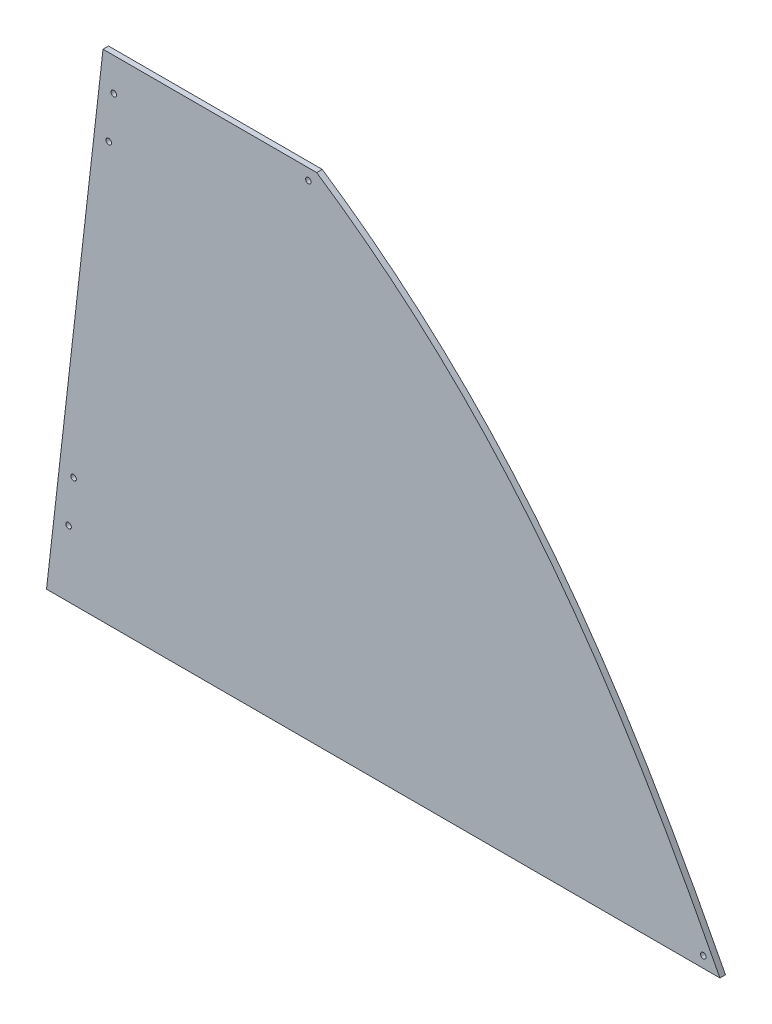
SolidWorks part; units mm, degrees
material "PC High Viscosity"
ref_plane "Front Plane" through (0, 0, 0) normal (0, 0, 1) x (1, 0, 0)
ref_plane "Top Plane" through (0, 0, 0) normal (0, 1, 0) x (1, 0, 0)
ref_plane "Right Plane" through (0, 0, 0) normal (1, 0, 0) x (0, 0, -1)
sketch "Sketch1" plane through (0, 0, 0) normal (0, 0, 1) x (1, 0, 0)
  line L0 (0, 0) -> (739.14, 0)
  line L1 (0, 0) -> (64.6956, 567.8263)
  line L2 (64.6956, 567.8263) -> (277.4206, 567.8263)
  spline S0 degree 3 poles (277.4206, 567.8263) (496.8592, 420.2971) (620.7582, 229.5902) (739.14, 0) knots 0 0 0 0 1 1 1 1
  dimension "D1" = 571.5
  dimension "D2" = 212.725
  dimension "D3" = 739.14
  dimension "D4" = 83.5
extrude "Boss-Extrude1" add sketch "Sketch1" along normal blind 6.35
sketch "Sketch2" plane through (0, 0, 0) normal (0, 0, -1) x (-1, 0, 0)
  line L0 (-295.925, 555.1263) -> (-63.2487, 555.1263) construction
  line L1 (-64.6956, 567.8263) -> (0, 0) construction
  line L2 (-277.4206, 567.8263) -> (-64.6956, 567.8263) construction
  line L3 (-732.5648, 12.7) -> (-1.447, 12.7) construction
  line L4 (0, 0) -> (-739.14, 0) construction
  spline S0 degree 3 poles (-739.14, 0) (-620.7582, 229.5902) (-496.8592, 420.2971) (-277.4206, 567.8263) knots 0 0 0 0 1 1 1 1 construction
  point P6 (-261, 555.1263)
  point P7 (-80.3937, 555.1263)
  point P14 (-707.1648, 12.7)
  point P15 (-26.847, 12.7)
  dimension "D1" = 12.7
  dimension "D2" = 17.145
  dimension "D3" = 34.925
  dimension "D4" = 12.7
  dimension "D5" = 25.4
  dimension "D6" = 25.4
hole_wizard "1/4 (0.25) Diameter Hole1" positions "Sketch3" profile "Sketch4" hole size "1/4" standard "ANSI Inch"
sketch "Sketch3" plane through (0, 0, 0) normal (0, 0, -1) x (-1, 0, 0)
  point P0 (-258.101, 541.9348)
  point P3 (-83.6862, 541.9348)
  point P7 (-704.6174, 12.7)
  point P10 (-26.9594, 12.7)
sketch "Sketch4" plane through (258.101, 541.9348, 0) normal (1, 0, 0) x (0, 1, 0)
  line L0 (0, 0) -> (0, 6.35)
  line L1 (0, 6.35) -> (3.175, 6.35)
  line L2 (3.175, 6.35) -> (3.175, 0)
  line L5 (3.175, 0) -> (0, 0)
  line L11 (0, -6.35) -> (0, 107.95) construction
  dimension "Thru Hole Dia." = 6.35
  dimension "Thru Hole Depth" = 6.35
sketch "Sketch5" plane through (0, 0, 0) normal (0, 0, -1) x (-1, 0, 0)
  line L0 (-64.6956, 567.8263) -> (-32.7402, 567.8263)
  line L1 (-32.7402, 567.8263) -> (31.9554, 0)
  line L2 (31.9554, 0) -> (0, 0)
  line L3 (-64.6956, 567.8263) -> (0, 0) construction
  line L4 (-64.6956, 567.8263) -> (0, 0)
  dimension "D1" = 31.75
extrude "Boss-Extrude2" add sketch "Sketch5" against normal up to surface (6.35 mm away)
sketch "Sketch6" plane through (0, 0, 6.35) normal (0, 0, 1) x (1, 0, 0)
  line L0 (49.357, 567.8263) -> (-15.3386, 0) construction
  line L1 (277.4206, 567.8263) -> (32.7402, 567.8263) construction
  line L2 (-31.9554, 0) -> (739.14, 0) construction
  line L3 (-31.9554, 0) -> (32.7402, 567.8263) construction
  point P8 (45.044, 529.9712)
  point P9 (39.2933, 479.4978)
  point P10 (-6.7125, 75.7102)
  point P11 (-0.9618, 126.1836)
  dimension "D1" = 16.51
  dimension "D2" = 50.8
  dimension "D3" = 38.1
  dimension "D4" = 50.8
  dimension "D5" = 76.2
hole_wizard "1/4 (0.25) Diameter Hole2" positions "Sketch7" profile "Sketch8" hole size "1/4" standard "ANSI Inch"
sketch "Sketch7" plane through (0, 0, 6.35) normal (0, 0, 1) x (1, 0, 0)
  point P0 (-6.7125, 75.7102)
  point P3 (-0.9618, 126.1836)
  point P6 (39.2933, 479.4978)
  point P9 (45.044, 529.9712)
sketch "Sketch8" plane through (-6.7125, 75.7102, 6.35) normal (1, 0, 0) x (0, -1, 0)
  line L0 (0, 0) -> (0, 8.2567)
  line L1 (0, 8.2567) -> (3.175, 6.349)
  line L2 (3.175, 6.349) -> (3.175, 0)
  line L5 (3.175, 0) -> (0, 0)
  line L10 (0, 8.2567) -> (-3.175, 6.349) construction
  line L11 (0, -6.35) -> (0, 107.95) construction
  dimension "Hole Dia." = 6.35
  dimension "Hole Depth" = 6.349
  dimension "Drill Angle" = 118
sketch "Sketch9" plane through (0, 0, 6.35) normal (0, 0, 1) x (1, 0, 0)
  line L0 (-31.9554, 0) -> (739.14, 0) construction
  line L1 (277.4206, 567.8263) -> (32.7402, 567.8263) construction
  point P0 (720.09, 12.7)
  point P4 (267.8956, 555.1263)
  dimension "D1" = 12.7
  dimension "D2" = 19.05
  dimension "D3" = 12.7
  dimension "D4" = 9.525
hole_wizard "1/4 (0.25) Diameter Hole3" positions "Sketch10" profile "Sketch12" hole size "1/4" standard "ANSI Inch" end condition up to next
sketch "Sketch10" plane through (0, 0, 6.35) normal (0, 0, 1) x (1, 0, 0)
  point P0 (720.09, 12.7)
  point P4 (267.8956, 555.1263)
sketch "Sketch12" plane through (720.09, 12.7, 6.35) normal (1, 0, 0) x (0, -1, 0)
  line L0 (0, 0) -> (0, 6.35)
  line L1 (0, 6.35) -> (3.175, 6.35)
  line L2 (3.175, 6.35) -> (3.175, 0)
  line L5 (3.175, 0) -> (0, 0)
  line L11 (0, -6.35) -> (0, 107.95) construction
  dimension "Thru Hole Dia." = 6.35
  dimension "Thru Hole Depth" = 6.35
